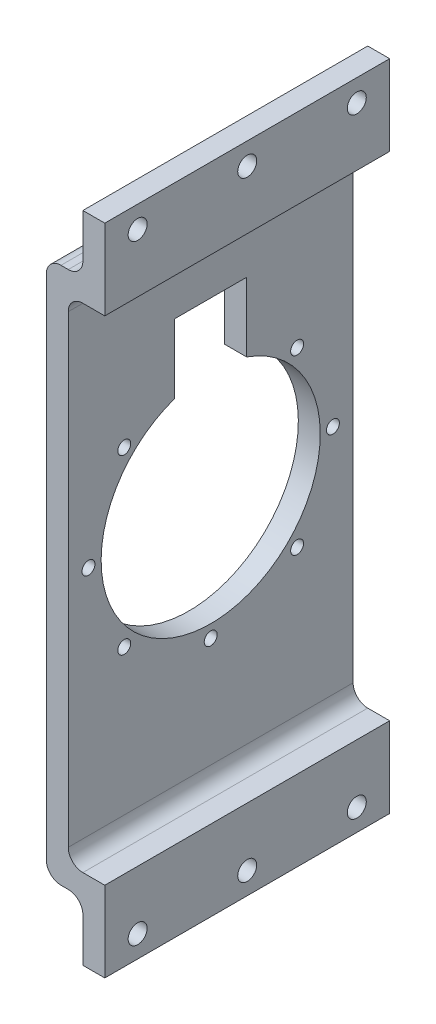
SolidWorks part; units mm, degrees
other "Markup1"
sketch "Sketch9" plane through (-7.62, -27.94, -49.53) normal (-1, 0, 0) x (0, 0, 1)
sketch "Sketch12" plane through (-7.62, -27.94, -49.53) normal (-1, 0, 0) x (0, 0, 1)
sketch "Sketch13" plane through (-7.62, -27.94, -49.53) normal (-1, 0, 0) x (0, 0, 1)
sketch "Sketch15" plane through (-7.62, -27.94, -49.53) normal (-1, 0, 0) x (0, 0, 1)
sketch "Sketch16" plane through (-7.62, -27.94, -49.53) normal (-1, 0, 0) x (0, 0, 1)
sketch "Sketch17" plane through (-7.62, -27.94, -49.53) normal (-1, 0, 0) x (0, 0, 1)
material "ABS"
ref_plane "Front Plane" through (0, 0, 0) normal (0, 0, 1) x (1, 0, 0)
ref_plane "Top Plane" through (0, 0, 0) normal (0, 1, 0) x (1, 0, 0)
ref_plane "Right Plane" through (0, 0, 0) normal (1, 0, 0) x (0, 0, -1)
sketch "Sketch1" plane through (0, 0, 0) normal (0, 0, 1) x (1, 0, 0)
  line L0 (0, 0) -> (0, 171.45)
  line L1 (0, 0) -> (12.7, 0)
  line L2 (-7.62, -7.62) -> (-7.62, 171.45)
  line L3 (-7.62, -7.62) -> (5.08, -7.62)
  line L5 (12.7, 0) -> (12.7, -7.62)
  line L8 (0, 171.45) -> (12.7, 171.45)
  line L9 (-7.62, 171.45) -> (-7.62, 179.07)
  line L10 (-7.62, 179.07) -> (5.08, 179.07)
  line L11 (12.7, 171.45) -> (12.7, 179.07)
  line L12 (12.7, -7.62) -> (12.7, -27.94)
  line L13 (12.7, -27.94) -> (5.08, -27.94)
  line L14 (5.08, -27.94) -> (5.08, -7.62)
  line L15 (12.7, 179.07) -> (12.7, 199.39)
  line L16 (-7.62, -7.62) -> (12.7, -7.62) construction
  line L17 (12.7, 199.39) -> (5.08, 199.39)
  line L18 (5.08, 199.39) -> (5.08, 179.07)
  dimension "D3" = 20.32
  dimension "D4" = 171.45
  dimension "D2" = 20.32
  dimension "D1" = 7.62
extrude "Boss-Extrude1" add sketch "Sketch1" along normal mid plane 99.06
ref_plane "Actuator Plane" through (0, 85.725, 0) normal (0, 1, 0) x (1, 0, 0)
fillet "Fillet1" radius 5.08 6 edges at (0, 0, 0) (5.08, -7.62, 0) (0, 171.45, 0) (5.08, 179.07, 0) (-7.62, 179.07, 0) (-7.62, -7.62, 0)
sketch "Sketch7" plane through (0, 0, 0) normal (1, 0, 0) x (0, 0, -1)
  line L0 (4.191, 85.725) -> (-4.191, 85.725) construction
  line L3 (-39.2649, 101.989) -> (0, 85.725) construction
  line L4 (0, 85.725) -> (-42.5, 85.725) construction
  circle A0 centre (0, 85.725) radius 42.5 construction
  circle A1 centre (-42.5, 85.725) radius 2.25
  circle A2 centre (-30.052, 115.777) radius 2.25
  circle A3 centre (0, 128.225) radius 2.25
  circle A4 centre (30.052, 115.777) radius 2.25
  circle A5 centre (42.5, 85.725) radius 2.25
  circle A6 centre (30.052, 55.673) radius 2.25
  circle A7 centre (0, 43.225) radius 2.25
  circle A8 centre (-30.052, 55.673) radius 2.25
  circle A9 centre (-39.2649, 101.989) radius 1.75 construction
  circle A10 centre (-16.264, 124.9899) radius 1.75 construction
  circle A11 centre (16.264, 124.9899) radius 1.75 construction
  circle A12 centre (39.2649, 101.989) radius 1.75 construction
  circle A13 centre (39.2649, 69.461) radius 1.75 construction
  circle A14 centre (16.264, 46.4601) radius 1.75 construction
  circle A15 centre (-16.264, 46.4601) radius 1.75 construction
  circle A16 centre (-39.2649, 69.461) radius 1.75 construction
  circle A17 centre (0, 85.725) radius 38.1
  point P28 (0, 85.725)
  point P45 (0, 85.725)
  dimension "D1" = 4.5
  dimension "D2" = 85
  dimension "D5" = 3.5
  dimension "D7" = 76.2
  dimension "D4" = 22.5
  dimension "D3" = 8
  dimension "D6" = 8
extrude "Cut-Extrude1" cut sketch "Sketch7" against normal up to surface (26.67 mm away)
sketch "Sketch8" plane through (5.08, 0, 0) normal (-1, 0, 0) x (0, 0, 1)
  line L0 (-38.1, 191.77) -> (0, 191.77) construction
  line L1 (0, 191.77) -> (38.1, 191.77) construction
  line L2 (0, -55) -> (0, 55) construction
  line L4 (-49.53, 199.39) -> (-49.53, 184.15) construction
  circle A0 centre (-38.1, 191.77) radius 3.302
  circle A1 centre (0, 191.77) radius 3.302
  circle A3 centre (38.1, 191.77) radius 3.302
  point P17 (-49.53, 191.77)
  dimension "D4" = 6.604
  dimension "D2" = 76.2
extrude "Cut-Extrude2" cut sketch "Sketch8" against normal up to surface (1.27 mm away)
mirror "Mirror1" about plane through (0, 85.725, 0) normal (0, 1, 0) of "Cut-Extrude2"
sketch "Sketch14" plane through (-7.62, 0, 0) normal (-1, 0, 0) x (0, 0, 1)
  line L0 (12.5, 121.7161) -> (12.5, 145.725)
  line L1 (12.5, 145.725) -> (-12.5, 145.725)
  line L2 (-12.5, 145.725) -> (-12.5, 121.7161)
  circle A0 centre (0, 85.725) radius 38.1 construction
  arc A1 (12.5, 121.7161) -> (-12.5, 121.7161) centre (0, 85.725) ccw
  point P10 (0, 145.725)
  dimension "D1" = 25
  dimension "D2" = 60
extrude "Cut-Extrude3" cut sketch "Sketch14" against normal up to surface (7.62 mm away) up to face at (0, 85.725, 40.25)
equation "\"VerticalHeight\"= 6.75"
equation "\"D4@Sketch1\"=\"VerticalHeight\""
